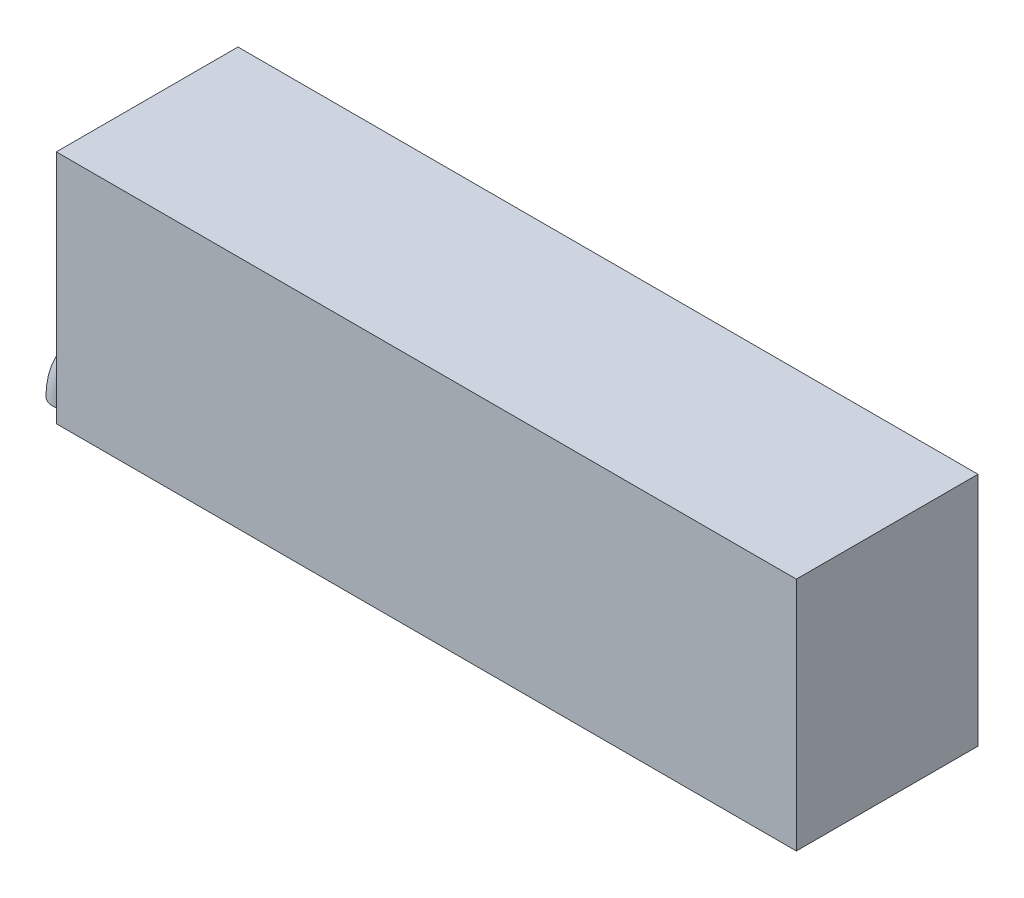
SolidWorks part; units mm, degrees
ref_plane "前基準面" through (0, 0, 0) normal (0, 0, 1) x (1, 0, 0)
ref_plane "上基準面" through (0, 0, 0) normal (0, 1, 0) x (1, 0, 0)
ref_plane "右基準面" through (0, 0, 0) normal (1, 0, 0) x (0, 0, -1)
sketch "草圖1" plane through (0, 0, 0) normal (0, 0, 1) x (1, 0, 0)
  line L1 (55, -17.5) -> (-55, -17.5)
  line L2 (55, -17.5) -> (55, 17.5)
  line L3 (55, 17.5) -> (-55, 17.5)
  line L4 (-55, -17.5) -> (-55, 17.5)
  line L5 (55, -17.5) -> (-55, 17.5) construction
  line L6 (55, 17.5) -> (-55, -17.5) construction
  point P0 (0, 0)
  dimension "D1" = 110
  dimension "D2" = 35
extrude "填料-伸長1" add sketch "草圖1" along normal mid plane 27
sketch "草圖2" plane through (-55, 0, 0) normal (-1, 0, 0) x (0, 0, 1)
  line L0 (-2.5, -15) -> (2.5, -15) construction
  line L1 (-2.5, -12.5) -> (2.5, -12.5)
  line L2 (-2.5, -17.5) -> (2.5, -17.5)
  line L3 (13.5, -17.5) -> (-13.5, -17.5) construction
  line L4 (-6.0795, -24.0054) -> (8.2081, -24.0054) construction
  arc A0 (-2.5, -12.5) -> (-2.5, -17.5) centre (-2.5, -15) ccw
  arc A1 (2.5, -17.5) -> (2.5, -12.5) centre (2.5, -15) ccw
  point P2 (0, -15)
  dimension "D1" = 5
  dimension "D2" = 5
revolve "旋轉1" add sketch "草圖2" angle 90 about L4
